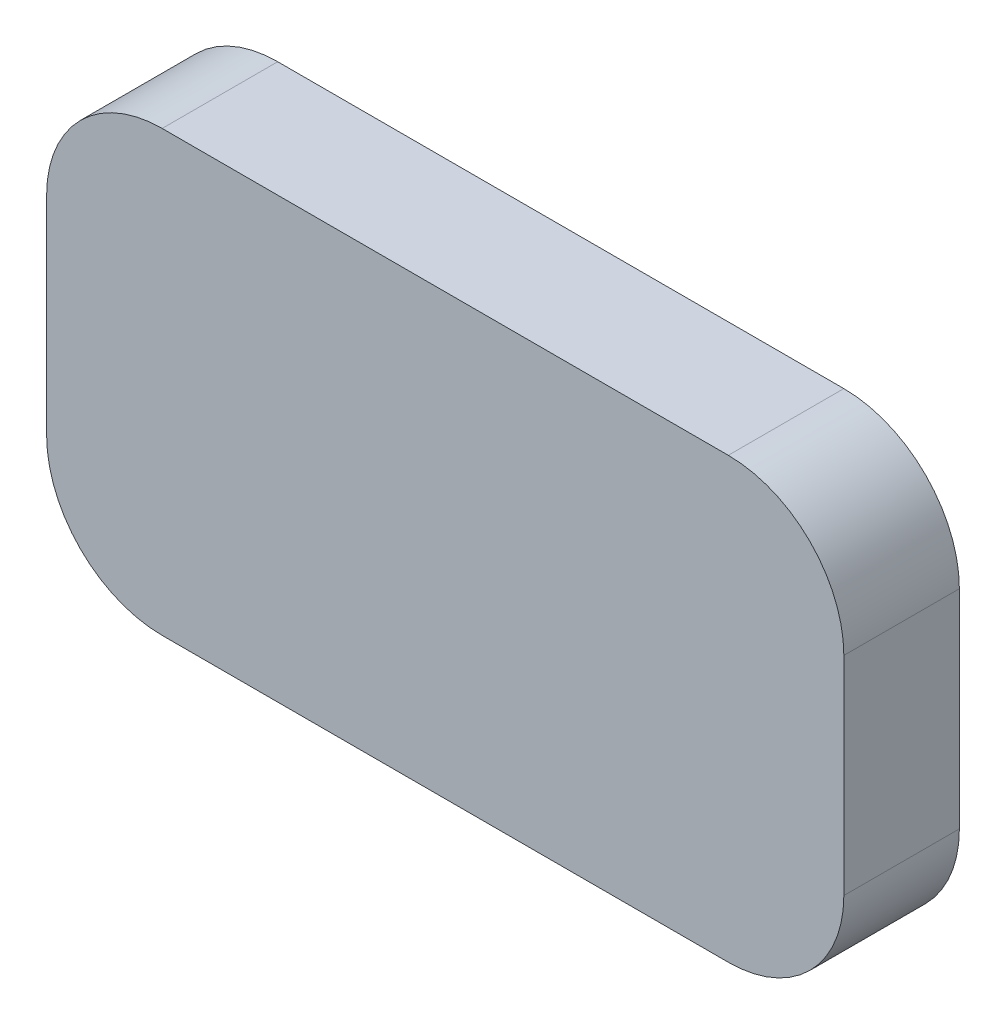
SolidWorks part; units mm, degrees
ref_plane "Front Plane" through (0, 0, 0) normal (0, 0, 1) x (1, 0, 0)
ref_plane "Top Plane" through (0, 0, 0) normal (0, 1, 0) x (1, 0, 0)
ref_plane "Right Plane" through (0, 0, 0) normal (1, 0, 0) x (0, 0, -1)
sketch "Sketch1" plane through (0, 0, 0) normal (0, 0, 1) x (1, 0, 0)
  line L1 (0, 0) -> (69, 0)
  line L2 (0, 0) -> (0, -38)
  line L3 (0, -38) -> (69, -38)
  line L4 (69, 0) -> (69, -38)
  dimension "D1" = 69
  dimension "D2" = 38
extrude "Boss-Extrude1" add sketch "Sketch1" along normal blind 10
fillet "Fillet1" radius 10 4 edges at (0, -38, 5) (0, 0, 5) (69, -38, 5) (69, 0, 5)
